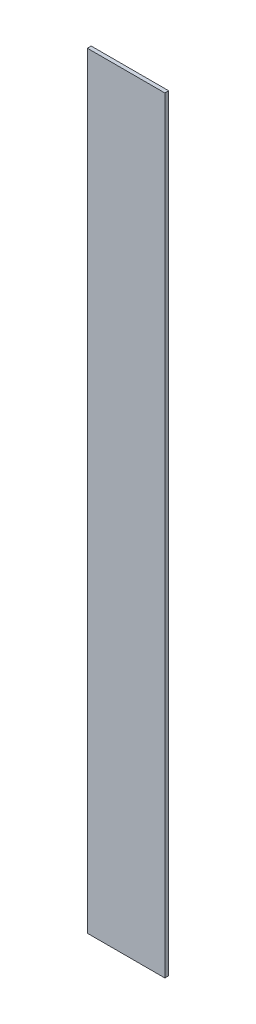
SolidWorks part; units mm, degrees
ref_plane "정면" through (0, 0, 0) normal (0, 0, 1) x (1, 0, 0)
ref_plane "윗면" through (0, 0, 0) normal (0, 1, 0) x (1, 0, 0)
ref_plane "우측면" through (0, 0, 0) normal (1, 0, 0) x (0, 0, -1)
sketch "스케치1" plane through (0, 0, 0) normal (0, 1, 0) x (1, 0, 0)
  line L1 (0, 0) -> (60.6585, 0)
  line L2 (0, 0) -> (0, 3)
  line L3 (0, 3) -> (60.6585, 3)
  line L4 (60.6585, 0) -> (60.6585, 3)
  dimension "D1" = 3
extrude "보스-돌출1" add sketch "스케치1" along normal blind 600
